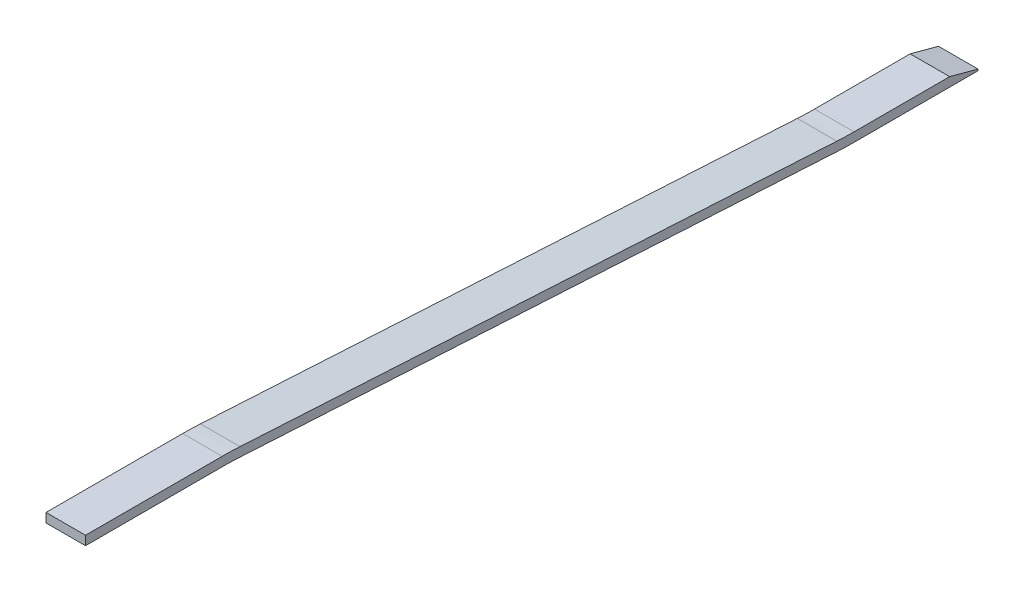
SolidWorks part; units mm, degrees
material "Cedar"
ref_plane "Front" through (0, 0, 0) normal (0, 0, 1) x (1, 0, 0)
ref_plane "Top" through (0, 0, 0) normal (0, 1, 0) x (1, 0, 0)
ref_plane "Right" through (0, 0, 0) normal (1, 0, 0) x (0, 0, -1)
sketch "Sketch1" plane through (0, 0, 0) normal (1, 0, 0) x (0, 0, -1)
  line L0 (55, 14) -> (100, 14)
  line L1 (105.6773, 13.8387) -> (302.1523, 2.6661)
  line L2 (308, 2.5) -> (348.8038, 2.5)
  line L3 (0, 0) -> (348.8038, 0) construction
  line L5 (55, 14) -> (55, 17)
  line L6 (55, 17) -> (100, 17)
  line L7 (105.8477, 16.8339) -> (302.3227, 5.6613)
  line L8 (308, 5.5) -> (339.4737, 5.5)
  line L9 (348.8038, 2.5) -> (348.8038, 3)
  line L10 (348.8038, 3) -> (339.4737, 5.5)
  line L11 (348.8038, 0) -> (360, 0) construction
  line L12 (360, 0) -> (348.8038, 3) construction
  arc A0 (100, 14) -> (105.6773, 13.8387) centre (100, -86) cw
  arc A1 (302.1523, 2.6661) -> (308, 2.5) centre (308, 105.5) ccw
  arc A2 (100, 17) -> (105.8477, 16.8339) centre (100, -86) cw
  arc A3 (302.3227, 5.6613) -> (308, 5.5) centre (308, 105.5) ccw
  dimension "D5" = 100
  dimension "D6" = 100
  dimension "D1" = 5
  dimension "D2" = 45
  dimension "D3" = 28
  dimension "D4" = 52
  dimension "D7" = 3
  dimension "D8" = 0.5
  dimension "D9" = 15
  dimension "D10" = 360
  dimension "D11" = 55
extrude "Extrude1" add sketch "Sketch1" along normal mid plane 13
